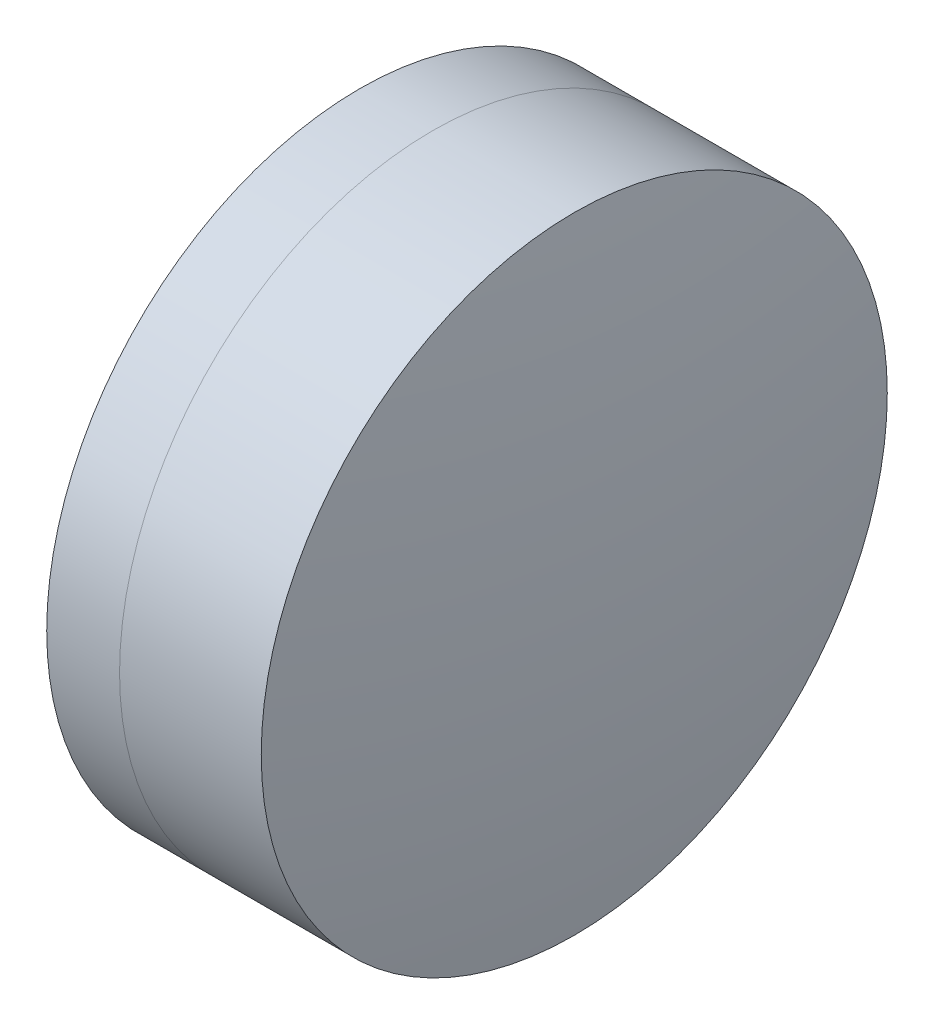
SolidWorks part; units mm, degrees
ref_plane "前视基准面" through (0, 0, 0) normal (0, 0, 1) x (1, 0, 0)
ref_plane "上视基准面" through (0, 0, 0) normal (0, 1, 0) x (1, 0, 0)
ref_plane "右视基准面" through (0, 0, 0) normal (1, 0, 0) x (0, 0, -1)
sketch "草图1" plane through (0, 0, 0) normal (0, 1, 0) x (1, 0, 0)
  line L0 (-9.7026, 0) -> (11.7646, 0) construction
  line L1 (-0.1821, -6.25) -> (1.2724, -6.25)
  line L2 (-0.1821, 6.25) -> (1.2724, 6.25)
  arc A0 (1.2724, -6.25) -> (1.2724, 6.25) centre (-11.8071, 0) ccw
  arc A1 (-0.1821, 6.25) -> (-0.1821, -6.25) centre (19.2789, 0) ccw
  point P10 (-1.1611, 0)
  point P11 (2.6889, 0)
  dimension "D3" = 20.44
  dimension "D4" = 14.496
  dimension "D1" = 6.25
  dimension "D2" = 6.25
  dimension "D5" = 3.85
revolve "旋转1" add sketch "草图1" angle 360 about L0
sketch "草图2" plane through (0, 0, 0) normal (0, 1, 0) x (1, 0, 0)
  line L0 (-0.5519, 0) -> (13.3053, 0) construction
  line L2 (1.2724, 6.25) -> (4.1014, 6.25)
  line L3 (1.2724, -6.25) -> (4.1014, -6.25)
  arc A0 (4.1014, -6.25) -> (4.1014, 6.25) centre (-36.5611, 0) ccw
  arc A1 (1.2724, -6.25) -> (1.2724, 6.25) centre (-11.8071, 0) ccw construction
  arc A2 (1.2724, -6.25) -> (1.2724, 6.25) centre (-11.8071, 0) ccw
  point P4 (2.6889, 0)
  point P8 (4.5789, 0)
  dimension "D1" = 41.14
  dimension "D2" = 1.89
revolve "旋转3" add sketch "草图2" angle 360 about L0
